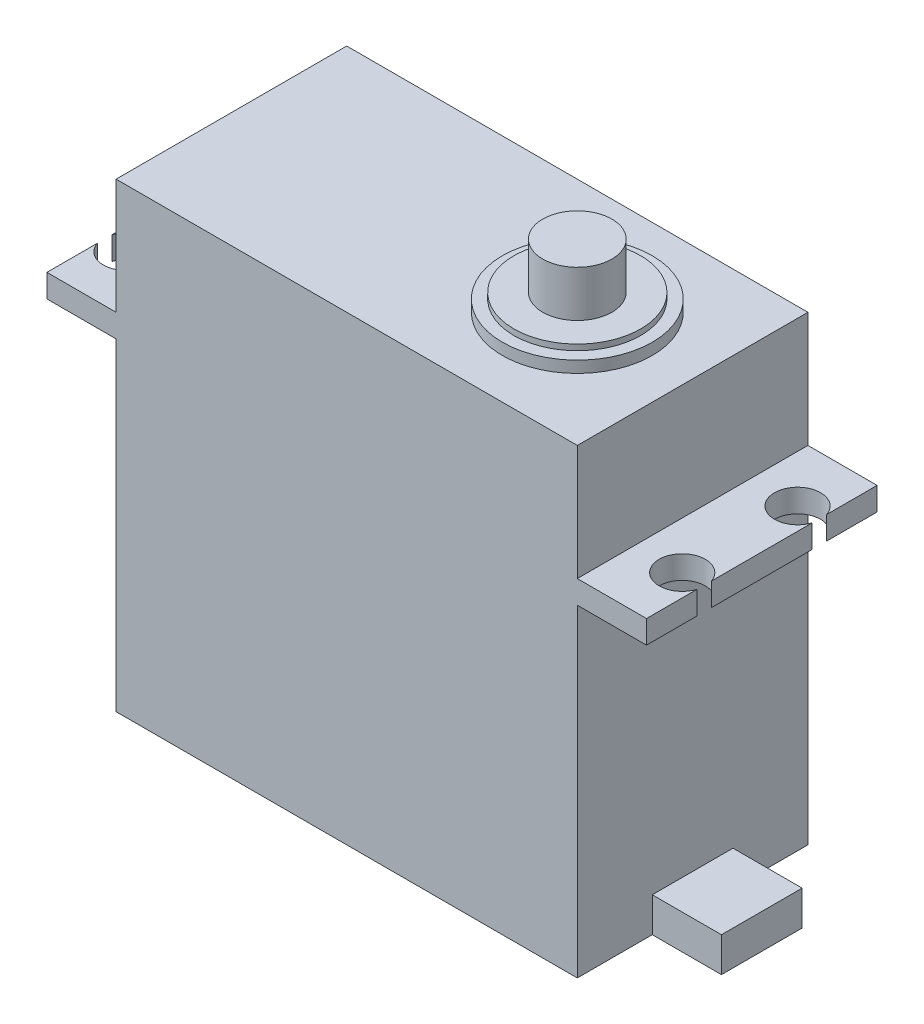
SolidWorks part; units mm, degrees
ref_plane "前视基准面" through (0, 0, 0) normal (0, 0, 1) x (1, 0, 0)
ref_plane "上视基准面" through (0, 0, 0) normal (0, 1, 0) x (1, 0, 0)
ref_plane "右视基准面" through (0, 0, 0) normal (1, 0, 0) x (0, 0, -1)
sketch "草图1" plane through (0, 0, 0) normal (0, 1, 0) x (1, 0, 0)
  line L1 (-20, -10) -> (20, -10)
  line L2 (-20, -10) -> (-20, 10)
  line L3 (-20, 10) -> (20, 10)
  line L4 (20, -10) -> (20, 10)
  line L5 (-20, -10) -> (20, 10) construction
  line L6 (-20, 10) -> (20, -10) construction
  point P0 (0, 0)
  dimension "D1" = 40
  dimension "D2" = 20
extrude "凸台-拉伸1" add sketch "草图1" along normal blind 40
sketch "草图2" plane through (20, 0, 0) normal (1, 0, 0) x (0, 0, -1)
  line L0 (-10, 40) -> (-10, 0) construction
  line L1 (-10, 30) -> (10, 30)
  line L2 (-10, 30) -> (-10, 28)
  line L3 (-10, 28) -> (10, 28)
  line L4 (10, 30) -> (10, 28)
  line L5 (10, 40) -> (10, 0) construction
  line L6 (0, 22) -> (0, -22) construction
  line L7 (-3.5, 3) -> (3.5, 3)
  line L8 (-3.5, 3) -> (-3.5, 0)
  line L9 (-3.5, 0) -> (3.5, 0)
  line L10 (3.5, 3) -> (3.5, 0)
  line L11 (11, 0) -> (-11, 0) construction
  line L12 (-10, 40) -> (10, 40) construction
  dimension "D1" = 7
  dimension "D2" = 3.5
  dimension "D3" = 3
  dimension "D4" = 12
  dimension "D5" = 2
extrude "凸台-拉伸2" add sketch "草图2" along normal blind 6
sketch "草图3" plane through (-20, 0, 0) normal (-1, 0, 0) x (0, 0, 1)
  line L0 (-10, 40) -> (-10, 0) construction
  line L1 (-10, 30) -> (10, 30)
  line L2 (-10, 30) -> (-10, 28)
  line L3 (-10, 28) -> (10, 28)
  line L4 (10, 30) -> (10, 28)
  line L5 (10, 40) -> (10, 0) construction
  line L6 (-10, 40) -> (10, 40) construction
  dimension "D1" = 2
  dimension "D2" = 12
extrude "凸台-拉伸3" add sketch "草图3" along normal blind 6
sketch "草图4" plane through (0, 30, 0) normal (0, 1, 0) x (1, 0, 0)
  line L0 (-22, 0) -> (22, 0) construction
  line L1 (26, 10) -> (26, -10) construction
  line L2 (-26, -10) -> (-26, 10) construction
  circle A0 centre (24.1, 5) radius 2
  circle A1 centre (24.1, -5) radius 2
  circle A2 centre (-24.1, 5) radius 2
  circle A3 centre (-24.1, -5) radius 2
  dimension "D1" = 4
  dimension "D4" = 4
  dimension "D7" = 4
  dimension "D8" = 4
  dimension "D2" = 5
  dimension "D3" = 5
  dimension "D5" = 1.9
  dimension "D6" = 1.9
  dimension "D9" = 10
  dimension "D10" = 5
  dimension "D11" = 1.9
  dimension "D12" = 1.9
extrude "切除-拉伸2" cut sketch "草图4" against normal blind 6
sketch "草图5" plane through (0, 40, 0) normal (0, 1, 0) x (1, 0, 0)
  line L0 (-22, 0) -> (22, 0) construction
  line L1 (20, -10) -> (20, 10) construction
  circle A0 centre (10, 0) radius 6.5
  dimension "D2" = 13
  dimension "D1" = 10
extrude "凸台-拉伸4" add sketch "草图5" along normal blind 1
sketch "草图6" plane through (0, 41, 0) normal (0, 1, 0) x (1, 0, 0)
  circle A0 centre (10, 0) radius 5.5
  dimension "D1" = 11
extrude "凸台-拉伸5" add sketch "草图6" along normal blind 0.5
sketch "草图7" plane through (0, 41.5, 0) normal (0, 1, 0) x (1, 0, 0)
  circle A0 centre (10, 0) radius 3
  dimension "D1" = 6
extrude "凸台-拉伸6" add sketch "草图7" along normal blind 4
